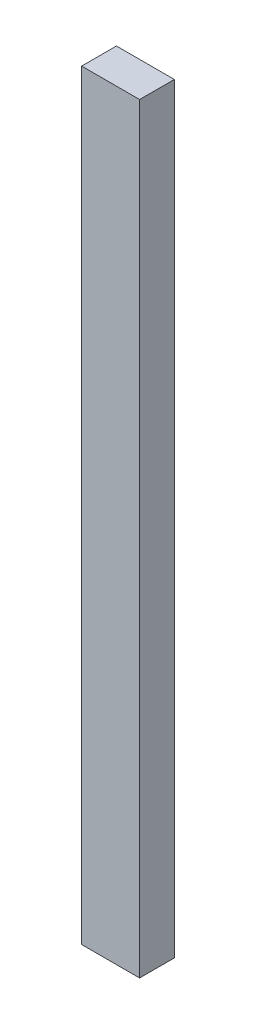
SolidWorks part; units mm, degrees
material "Balsa"
ref_plane "Front Plane" through (0, 0, 0) normal (0, 0, 1) x (1, 0, 0)
ref_plane "Top Plane" through (0, 0, 0) normal (0, 1, 0) x (1, 0, 0)
ref_plane "Right Plane" through (0, 0, 0) normal (1, 0, 0) x (0, 0, -1)
sketch "Sketch1" plane through (0, 0, 0) normal (0, 0, 1) x (1, 0, 0)
  line L1 (-15, 197) -> (15, 197)
  line L2 (-15, 197) -> (-15, -197)
  line L3 (-15, -197) -> (15, -197)
  line L4 (15, 197) -> (15, -197)
  line L5 (-15, 197) -> (15, -197) construction
  line L6 (-15, -197) -> (15, 197) construction
  point P0 (0, 0)
  dimension "D1" = 30
  dimension "D2" = 394
extrude "Boss-Extrude1" add sketch "Sketch1" along normal blind 18
